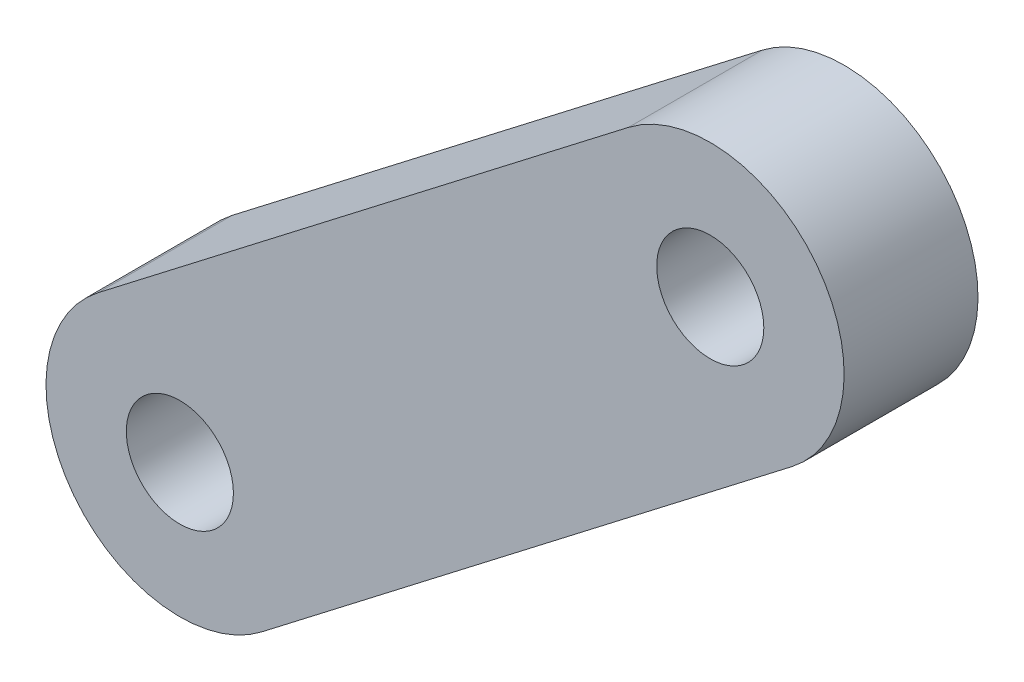
SolidWorks part; units mm, degrees
ref_plane "Front Plane" through (0, 0, 0) normal (0, 0, 1) x (1, 0, 0)
ref_plane "Top Plane" through (0, 0, 0) normal (0, 1, 0) x (1, 0, 0)
ref_plane "Right Plane" through (0, 0, 0) normal (1, 0, 0) x (0, 0, -1)
sketch "Sketch1" plane through (0, 0, 0) normal (0, 0, 1) x (0.9998, -0.022, 0)
  line L0 (-41.8829, 111.4723) -> (-17.0715, 91.626) construction
  line L1 (-1.7639, 79.3817) -> (-1.7639, 99.3817) construction
  line L2 (-1.7639, 99.3817) -> (-51.7712, 99.3817) construction
  line L3 (-46.2352, 83.6971) -> (-26.7675, 99.3817) construction
  line L4 (-46.2352, 83.6971) -> (-49.3722, 87.5906) construction
  line L5 (-49.3722, 87.5906) -> (-43.0983, 79.8035) construction
  line L6 (-49.3722, 87.5906) -> (-29.9044, 103.2753)
  line L7 (-43.0983, 79.8035) -> (-23.6306, 95.4882)
  line L8 (-29.9044, 103.2753) -> (-23.6306, 95.4882) construction
  circle A0 centre (-1.7639, 79.3817) radius 2.5 construction
  circle A1 centre (-1.7639, 79.3817) radius 2.5 construction
  circle A3 centre (-26.7675, 99.3817) radius 2
  arc A4 (-22.8629, 96.2585) -> (-30.6611, 96.2448) centre (-26.7675, 99.3817) ccw
  circle A5 centre (-46.2352, 83.6971) radius 2 construction
  circle A6 centre (-46.2352, 83.6971) radius 2
  arc A7 (-49.3722, 87.5906) -> (-43.0983, 79.8035) centre (-46.2352, 83.6971) ccw
  arc A8 (-23.6306, 95.4882) -> (-29.9044, 103.2753) centre (-26.7675, 99.3817) ccw
  point P18 (-26.7675, 99.3817)
  dimension "D1" = 5
  dimension "D2" = 5
  dimension "D4" = 4
  dimension "D5" = 4
  dimension "D6" = 10
  dimension "D3" = 20
  dimension "D7" = 25
extrude "Boss-Extrude1" add sketch "Sketch1" along normal blind 5
sketch "Sketch2" plane through (0, 0, 0) normal (0, 0, -1) x (-1, 0, 0)
  circle A0 centre (44.3801, 84.6953) radius 2
